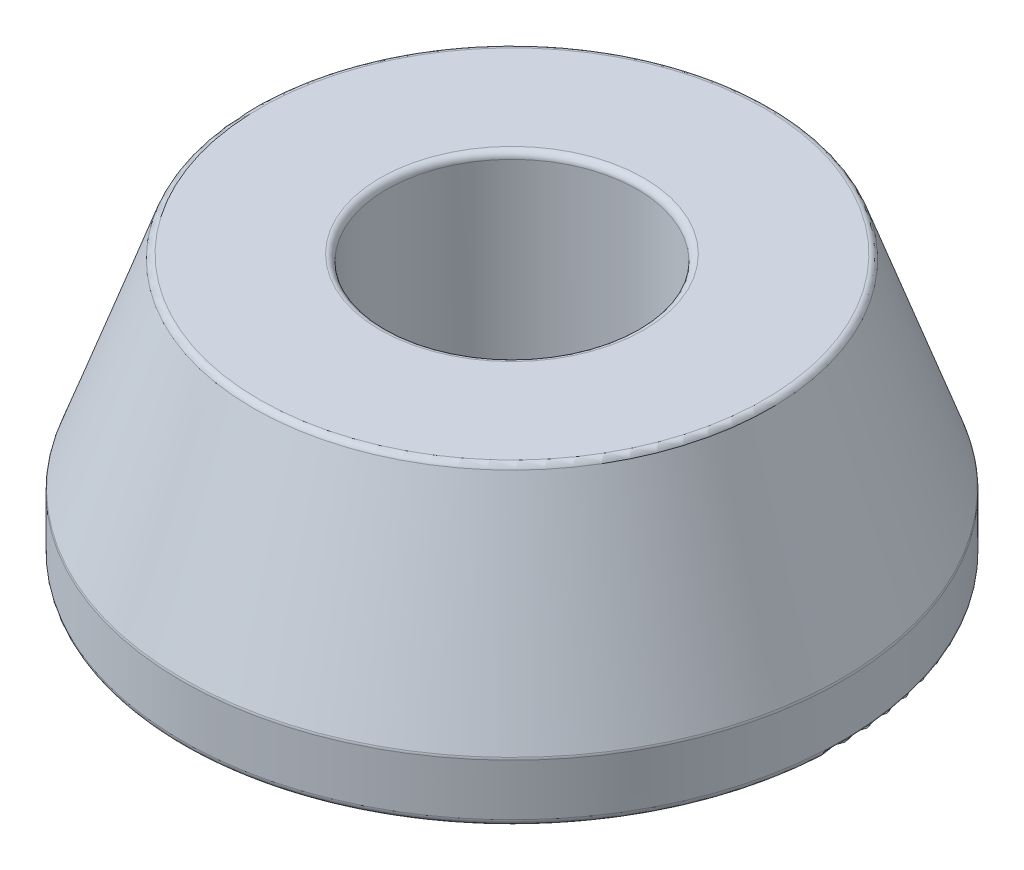
SolidWorks part; units mm, degrees
ref_plane "Front Plane" through (0, 0, 0) normal (0, 0, 1) x (1, 0, 0)
ref_plane "Top Plane" through (0, 0, 0) normal (0, 1, 0) x (1, 0, 0)
ref_plane "Right Plane" through (0, 0, 0) normal (1, 0, 0) x (0, 0, -1)
sketch "Sketch1" plane through (0, 0, 0) normal (0, 0, 1) x (1, 0, 0)
  line L0 (0, 0) -> (0, 10) construction
  line L1 (4.75, 10) -> (9.75, 10)
  line L2 (9.75, 10) -> (12.5, 2.25)
  line L3 (12.5, 2.25) -> (12.5, 0)
  line L4 (12.5, 0) -> (4.75, 0)
  line L5 (4.75, 10) -> (4.75, 0)
  dimension "D1" = 10
  dimension "D2" = 4.75
  dimension "D3" = 12.5
  dimension "D4" = 9.75
  dimension "D5" = 2.25
revolve "Revolve1" add sketch "Sketch1" angle 360 about L0
fillet "Fillet1" radius 0.25 5 edges at (0, 10, -4.75) (0, 0, -4.75) (0, 0, -12.5) (0, 2.25, -12.5) (0, 10, -9.75)
